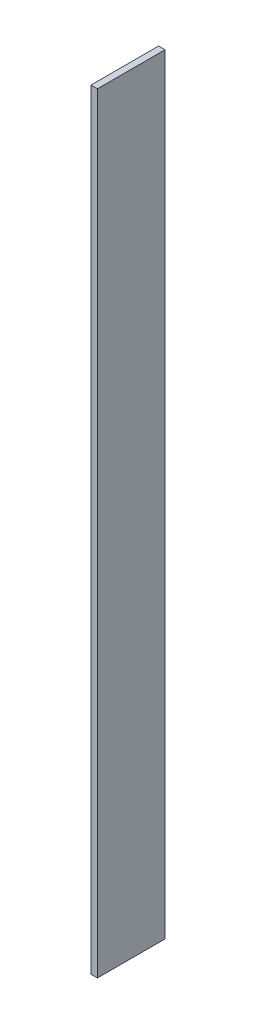
SolidWorks part; units mm, degrees
ref_plane "Front Plane" through (0, 0, 0) normal (0, 0, 1) x (1, 0, 0)
ref_plane "Top Plane" through (0, 0, 0) normal (0, 1, 0) x (1, 0, 0)
ref_plane "Right Plane" through (0, 0, 0) normal (1, 0, 0) x (0, 0, -1)
sketch "Sketch1" plane through (0, 0, 0) normal (1, 0, 0) x (0, 0, -1)
  line L1 (-6.35, -72.2312) -> (6.35, -72.2312)
  line L2 (-6.35, -72.2312) -> (-6.35, 72.2313)
  line L3 (-6.35, 72.2313) -> (6.35, 72.2313)
  line L4 (6.35, -72.2312) -> (6.35, 72.2313)
  line L5 (-6.35, -72.2312) -> (6.35, 72.2313) construction
  line L6 (-6.35, 72.2313) -> (6.35, -72.2312) construction
  point P0 (0, 0)
  dimension "D1" = 12.7
  dimension "D2" = 144.4625
extrude "Boss-Extrude1" add sketch "Sketch1" along normal blind 1.2141
